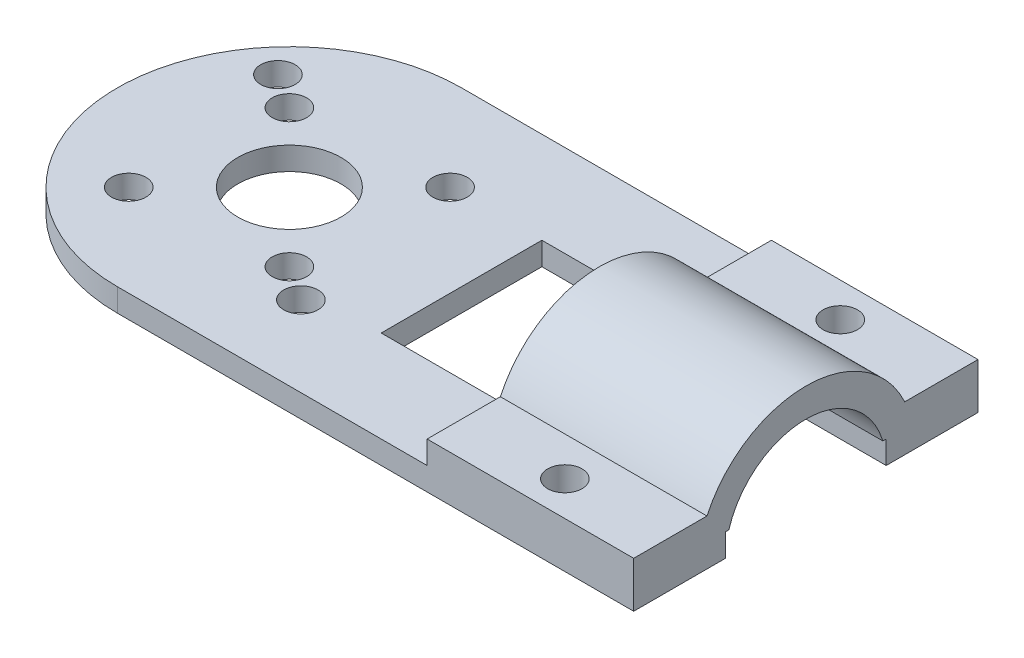
SolidWorks part; units mm, degrees
material "Plástico personalizado"
ref_plane "Plano frontal" through (0, 0, 0) normal (0, 0, 1) x (1, 0, 0)
ref_plane "Plano superior" through (0, 0, 0) normal (0, 1, 0) x (1, 0, 0)
ref_plane "Plano direito" through (0, 0, 0) normal (1, 0, 0) x (0, 0, -1)
sketch "Esboço1" plane through (0, 0, 0) normal (0, 1, 0) x (1, 0, 0)
  line L0 (30, 15) -> (30, 7)
  line L1 (-15, -15) -> (30, -15)
  line L2 (30, -7) -> (30, -15)
  line L3 (-15, 15) -> (30, 15)
  line L4 (30, 7) -> (0, 7)
  line L6 (30, -7) -> (0, -7)
  line L7 (0, 7) -> (0, -7)
  circle A0 centre (-15, 0) radius 4.5
  circle A1 centre (-9, -6) radius 1.5
  arc A2 (-15, 15) -> (-15, -15) centre (-15, 0) ccw
  circle A3 centre (-6, -8) radius 1.5
  circle A4 centre (-22, -7) radius 1.5
  circle A5 centre (-21, 6) radius 1.5
  circle A6 centre (-24, 8) radius 1.5
  circle A7 centre (-8, 7) radius 1.5
  point P0 (0, 0)
  point P6 (-30, 0)
  point P11 (0, 0)
  dimension "D5" = 9
  dimension "D7" = 30
  dimension "D10" = 3
  dimension "D1" = 30
  dimension "D2" = 30
  dimension "D3" = 14
  dimension "D4" = 9
  dimension "D6" = 8
  dimension "D8" = 6
  dimension "D9" = 6
  dimension "D11" = 7
  dimension "D12" = 7
  dimension "D13" = 6
  dimension "D14" = 6
  dimension "D15" = 8
  dimension "D16" = 9
  dimension "D17" = 7
  dimension "D18" = 7
extrude "Ressalto-extrusão1" add sketch "Esboço1" along normal blind 2
sketch "Esboço2" plane through (30, 0, 0) normal (1, 0, 0) x (0, 0, -1)
  line L0 (-15, 2) -> (-15, 4)
  line L1 (-15, 4) -> (-8.6168, 4)
  line L2 (15, 4) -> (15, 2)
  line L3 (15, 2) -> (-15, 2)
  line L4 (8.6168, 4) -> (15, 4)
  arc A0 (8.6168, 4) -> (-8.6168, 4) centre (0, 0) ccw
  dimension "D2" = 9.5
  dimension "D1" = 2
extrude "Ressalto-extrusão2" add sketch "Esboço2" against normal blind 18
sketch "Esboço3" plane through (30, 0, 0) normal (1, 0, 0) x (0, 0, -1)
  circle A0 centre (0, 0) radius 7
  dimension "D1" = 14
extrude "Corte-extrusão1" cut sketch "Esboço3" against normal blind 18
sketch "Esboço4" plane through (0, 4, 0) normal (0, 1, 0) x (1, 0, 0)
  line L0 (12, -15) -> (30, -15) construction
  line L1 (30, -8.6168) -> (30, -15) construction
  line L2 (12, 15) -> (30, 15) construction
  circle A0 centre (21, 12) radius 1.5
  circle A1 centre (21, -12) radius 1.5
  dimension "D1" = 3
  dimension "D2" = 9
  dimension "D3" = 3
  dimension "D4" = 3
extrude "Corte-extrusão2" cut sketch "Esboço4" against normal blind 17
